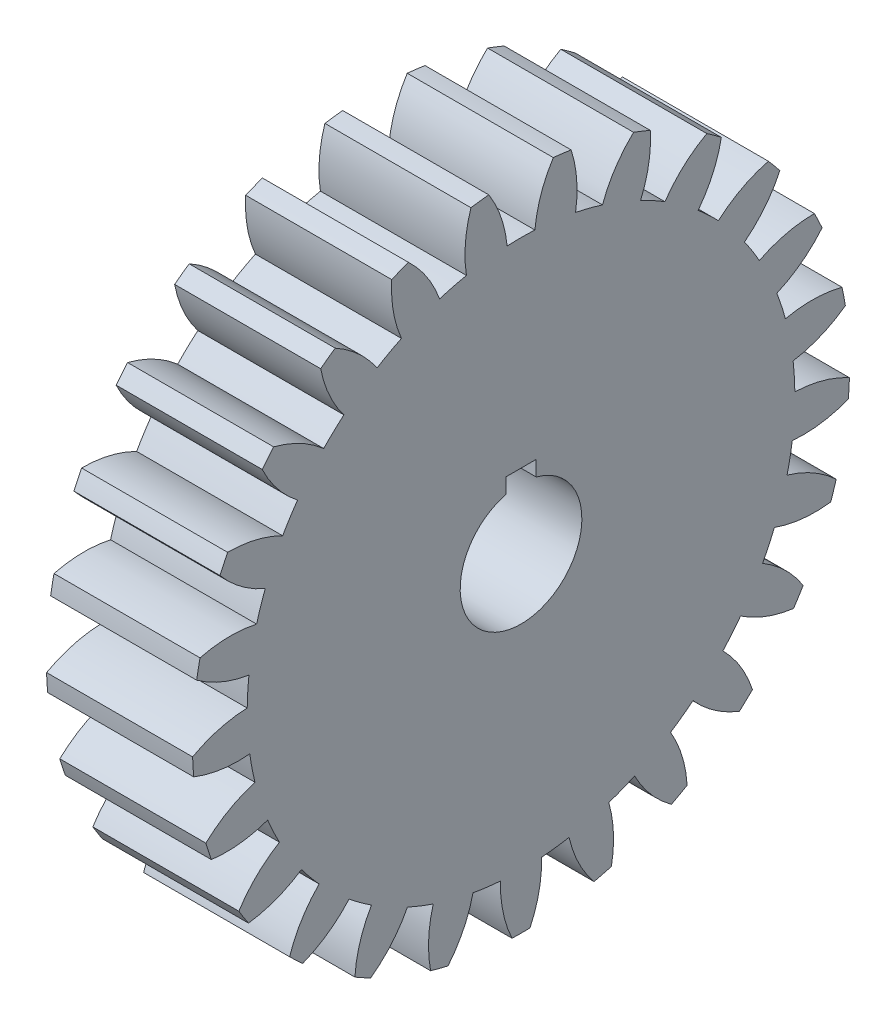
SolidWorks part; units mm, degrees
ref_plane "Plane1" through (0, 0, 0) normal (0, 0, 1) x (1, 0, 0)
ref_plane "Plane2" through (0, 0, 0) normal (0, 1, 0) x (1, 0, 0)
ref_plane "Plane3" through (0, 0, 0) normal (1, 0, 0) x (0, 0, -1)
other "Configuration Table"
sketch "HoldingSke" plane through (0, 0, 0) normal (0, 1, 0) x (1, 0, 0)
  line L0 (0, 0) -> (11.5101, -5.3673)
  line L1 (-15, 0) -> (100, 0) construction
  line L2 (0, 0) -> (-2.1039, 2.3779)
  line L3 (0, 0) -> (-11.863, 4.5341)
  line L4 (0, 0) -> (7.8269, 3.6497)
  line L5 (0, 0) -> (-47.5972, -17.7524)
  line L6 (0, 0) -> (-252.6679, -170.4757)
  line L7 (-2.1039, 2.3779) -> (63.5041, 300.0332)
  line L8 (-76.2, 54.61) -> (205.6384, 54.61)
  line L9 (-67.7845, 28.3722) -> (-49.3413, 33.142)
  line L10 (-76.2, 71.12) -> (104.1128, 71.12)
  line L11 (0, 0) -> (-304.8, 0)
  line L12 (-76.2, 101.6) -> (-74.295, 101.6)
  line L13 (24.9733, 27.94) -> (52.9518, 28.4284)
  line L14 (24.9733, 27.94) -> (24.9746, 27.94)
  line L15 (24.9733, 27.94) -> (100.4006, 29.5858)
  circle A0 centre (0, 0) radius 127
  circle A1 centre (0, 0) radius 38.1
  circle A2 centre (0, 0) radius 38.1
  circle A3 centre (0, 0) radius 127
  dimension "MHD" = 76.2
  dimension "Hub_dia" = 76.2
  dimension "Bore" = 254
  dimension "MBD" = 254
  dimension "Num_teeth" = 25
  dimension "Pitch" = 12.7
  dimension "Overall_len" = 50.8
  dimension "Show_teeth" = 25
  dimension "Thickness" = 304.8
  dimension "OAL" = 304.8001
  dimension "T_dim" = 281.8384
  dimension "Ap" = 14.5
  dimension "H" = 19.05
  dimension "Pitch_radius" = 180.3128
  dimension "Width" = 304.8
  dimension "Backlash" = 1.905
  dimension "Addendum_fac" = 1
  dimension "Dedendum_fac" = 1.25
  dimension "Clearance_fac" = 0.25
  dimension "Dedendum_add" = 0.0013
sketch "BasProSke" plane through (0, 0, 0) normal (0, 1, 0) x (1, 0, 0)
  line L0 (-10, 0) -> (60, 0) construction
  line L1 (0, 0) -> (0, 685.8)
  line L2 (0, 0) -> (304.8, 0)
  line L3 (304.8, 0) -> (304.8, 685.8)
  line L4 (304.8, 685.8) -> (0, 685.8)
  dimension "Thickness" = 304.8
  dimension "Diameter" = 1371.6
revolve "Base-Revolve" add sketch "BasProSke" angle 360 about L0
sketch "TooCutSke" plane through (0, 0, 0) normal (1, 0, 0) x (0, 0, -1)
  line L1 (0, 0) -> (0, 107) construction
  line L2 (0, 0) -> (-43.2046, 633.5285) construction
  line L3 (0, 0) -> (-158.9095, 1257.8981) construction
  line L4 (-43.2046, 633.5285) -> (-79.4547, 628.949) construction
  arc A0 (28.9619, 570.7644) -> (-28.9619, 570.7644) centre (0, 0) ccw
  arc A1 (67.344, 682.511) -> (-67.344, 682.511) centre (0, 0) ccw
  circle A2 centre (0, 0) radius 635 construction
  circle A3 centre (0, 0) radius 614.7738 construction
  arc A4 (-28.9619, 570.7644) -> (-67.344, 682.511) centre (-281.7896, 546.3894) ccw
  arc A5 (67.344, 682.511) -> (28.9619, 570.7644) centre (281.7896, 546.3894) ccw
  dimension "Root_dia" = 1142.9975
  dimension "Overcut_dia" = 1371.6508
  dimension "Pitch_dia" = 1270
  dimension "Base_dia" = 1229.5475
  dimension "Flank_rad" = 254
  dimension "Half_ang" = 7.2
  dimension "Half_CT" = 36.5382
extrude "ToothCut" cut sketch "TooCutSke" along normal through all
fillet "Breaks" [suppressed] radius 1.016
fillet "RootFillets" [suppressed] radius 12.7013
pattern_circular "TeethCuts" count 25 every 14.4 about axis through (-10, 0, 0) along (1, 0, 0) of "ToothCut", "RootFillets", "Breaks"
sketch "HubNeaOneSke" plane through (0, 0, 0) normal (-1, 0, 0) x (0, 0, 1)
  circle A0 centre (0, 0) radius 38.1
  dimension "Diameter" = 76.2
extrude "HubNearOne" [suppressed] add sketch "HubNeaOneSke" along normal blind 25.4001
sketch "HubNeaBotSke" plane through (0, 0, 0) normal (-1, 0, 0) x (0, 0, 1)
  circle A0 centre (0, 0) radius 38.1
  dimension "Diameter" = 76.2
extrude "HubNearBoth" [suppressed] add sketch "HubNeaBotSke" along normal blind 12.7
ref_plane "FarPln" through (304.8, 0, 0) normal (1, 0, 0) x (0, 0, -1)
sketch "HubFarSke" plane through (304.8, 0, 0) normal (1, 0, 0) x (0, 0, -1)
  circle A0 centre (0, 0) radius 38.1
  dimension "Diameter" = 76.2
extrude "HubFar" [suppressed] add sketch "HubFarSke" along normal blind 12.7
sketch "BorSke" plane through (0, 0, 0) normal (1, 0, 0) x (0, 0, -1)
  circle A0 centre (0, 0) radius 127
  dimension "Diameter" = 254
extrude "Bore" cut sketch "BorSke" along normal mid plane 609.6001
sketch "KeySke" plane through (0, 0, 0) normal (1, 0, 0) x (0, 0, -1)
  line L0 (-31.75, 0) -> (-31.75, 154.8384)
  line L1 (-31.75, 154.8384) -> (31.75, 154.8384)
  line L2 (31.75, 154.8384) -> (31.75, 0)
  line L3 (0, 0) -> (0, 34) construction
  line L4 (-31.75, 0) -> (31.75, 0)
  dimension "Offset" = 154.8384
  dimension "Width" = 63.5
extrude "Keyway" cut sketch "KeySke" along normal mid plane 609.6001
pattern_circular "Keyway2" [suppressed] count 2 every 90 about axis through (-10, 0, 0) along (1, 0, 0)
equation "' \"Pitch@HoldingSke\" = 4"
equation "' \"Num_teeth@HoldingSke\" = 12"
equation "' \"Ap@HoldingSke\" =  20"
equation "' \"Ap@HoldingSke\" = 20"
equation "' \"Width@HoldingSke\" = 0.5"
equation "' \"Hub_dia@HoldingSke\"= 1"
equation "' \"Hub_dia@HoldingSke\" = 1"
equation "' \"Overall_len@HoldingSke\" = 1.0"
equation "' \"Bore@HoldingSke\" = 0.75"
equation "' \"T_dim@HoldingSke\" = 0.85"
equation "' \"Width@KeySke\" = 0.25"
equation "' \"Show_teeth@HoldingSke\" = 13"
equation "' \"Backlash@HoldingSke\" = 0.009"
equation "' \"Addendum_fac@HoldingSke\" = 1.0"
equation "' \"Dedendum_fac@HoldingSke\" = 1.25"
equation "' \"Dedendum_add@HoldingSke\" = 0.00005"
equation "' \"Clearance_fac@HoldingSke\" = 0.25"
equation "' \"Pitch@HoldingSke\" = 0.5"
equation "' \"Num_teeth@HoldingSke\" = 23"
equation "' \"Show_teeth@HoldingSke\" = 23"
equation "' \"Backlash@HoldingSke\" = 0.0375"
equation "\"Overcut_dia@TooCutSke\" = (\"Num_teeth@HoldingSke\" + 2 * \"Addendum_fac@HoldingSke\") / \"Pitch@HoldingSke\" + 0.002"
equation "\"Pitch_dia@TooCutSke\" = \"Num_teeth@HoldingSke\" / \"Pitch@HoldingSke\""
equation "\"Base_dia@TooCutSke\" = \"Num_teeth@HoldingSke\" / \"Pitch@HoldingSke\" * cos((\"Ap@HoldingSke\"  * 3.14159265 / 180))"
equation "\"Root_dia@TooCutSke\" = (\"Num_teeth@HoldingSke\" + 2) / \"Pitch@HoldingSke\" - 2 * (\"Addendum_fac@HoldingSke\" + \"Dedendum_fac@HoldingSke\") / \"Pitch@HoldingSke\" - \"Dedendum_add@HoldingSke\" * 2"
equation "\"Half_ang@TooCutSke\" = 180 / \"Num_teeth@HoldingSke\""
equation "\"Half_CT@TooCutSke\" = \"Num_teeth@HoldingSke\" / \"Pitch@HoldingSke\" * sin((3.14159265 / 2 / \"Num_teeth@HoldingSke\")) / 2 - 7 * \"Backlash@HoldingSke\" / 4"
equation "\"Flank_rad@TooCutSke\" = \"Num_teeth@HoldingSke\" / \"Pitch@HoldingSke\" / 5"
equation "\"Radius@RootFillets\" = \"Clearance_fac@HoldingSke\" / \"Pitch@HoldingSke\" + \"Dedendum_add@HoldingSke\""
equation "\"Break_rad@Breaks\" = 0.02 / \"Pitch@HoldingSke\""
equation "\"Thickness@HoldingSke\" = \"Width@HoldingSke\""
equation "\"OAL@HoldingSke\" = \"Thickness@HoldingSke\""
equation "\"MHD@HoldingSke\" = (\"Num_teeth@HoldingSke\" + 2) / \"Pitch@HoldingSke\" - 2 * (\"Addendum_fac@HoldingSke\" + \"Dedendum_fac@HoldingSke\")  / \"Pitch@HoldingSke\" - \"Dedendum_add@HoldingSke\" * 2"
equation "\"MBD@HoldingSke\" = (\"Num_teeth@HoldingSke\" + 2) / \"Pitch@HoldingSke\" - 2 * (\"Addendum_fac@HoldingSke\" + \"Dedendum_fac@HoldingSke\")  / \"Pitch@HoldingSke\" - \"Dedendum_add@HoldingSke\" * 2 - 0.002"
equation "\"MHD@HoldingSke\" = ((sgn( \"MHD@HoldingSke\" - \"Hub_dia@HoldingSke\" )-1)*( \"MHD@HoldingSke\" - \"Hub_dia@HoldingSke\" ))/-2+ \"Hub_dia@HoldingSke\""
equation "\"MBD@HoldingSke\" = ((sgn( \"MBD@HoldingSke\" - \"Bore@HoldingSke\" )-1)*( \"MBD@HoldingSke\" - \"Bore@HoldingSke\" ))/-2+ \"Bore@HoldingSke\""
equation "\"OAL@HoldingSke\" = ((sgn( \"OAL@HoldingSke\" - \"Overall_len@HoldingSke\" )+1)*( \"OAL@HoldingSke\" - \"Overall_len@HoldingSke\" ))/2 + \"Overall_len@HoldingSke\" + 0.000002"
equation "\"Num_teeth@TeethCuts\" = int( \"Show_teeth@HoldingSke\" ) + 1"
equation "\"Num_teeth@TeethCuts\" = ((sgn( \"Num_teeth@TeethCuts\" - \"Num_teeth@HoldingSke\" )-1)*( \"Num_teeth@TeethCuts\" - \"Num_teeth@HoldingSke\" ))/-2+ \"Num_teeth@HoldingSke\""
equation "\"Num_teeth@TeethCuts\" = ((sgn( \"Num_teeth@TeethCuts\" - 2.0)+1)*( \"Num_teeth@TeethCuts\" - 2.0))/2 +2.0"
equation "\"Angle@TeethCuts\" = 360.0 / \"Num_teeth@HoldingSke\""
equation "\"Diameter@BasProSke\" = (\"Num_teeth@HoldingSke\" + 2 * \"Addendum_fac@HoldingSke\") / \"Pitch@HoldingSke\""
equation "\"Thickness@BasProSke\"  = \"Thickness@HoldingSke\""
equation "' \"Fillet_rad@BasProSke\" =  \"Thickness@HoldingSke\" * 0.05"
equation "' \"Fillet_rad@BasProSke\" = \"Thickness@HoldingSke\" * 0.05"
equation "\"MHD@HoldingSke\" = ((sgn( \"MHD@HoldingSke\" - \"Root_dia@TooCutSke\" )-1)*( \"MHD@HoldingSke\" - \"Root_dia@TooCutSke\" ))/-2+ \"Root_dia@TooCutSke\""
equation "\"Diameter@HubNeaOneSke\" = \"MHD@HoldingSke\""
equation "\"Length@HubNearOne\" = \"OAL@HoldingSke\" - \"Thickness@BasProSke\""
equation "\"Diameter@HubNeaBotSke\" = \"MHD@HoldingSke\""
equation "\"Length@HubNearBoth\" = ( \"OAL@HoldingSke\" - \"Thickness@BasProSke\" ) / 2.0"
equation "\"Thickness@FarPln\" = \"Thickness@BasProSke\""
equation "\"Diameter@HubFarSke\" = \"MHD@HoldingSke\""
equation "\"Length@HubFar\" = ( \"OAL@HoldingSke\" - \"Thickness@BasProSke\" ) / 2.0"
equation "\"Diameter@BorSke\" = \"MBD@HoldingSke\""
equation "\"D1@Bore\" = \"OAL@HoldingSke\" * 2.0"
equation "\"D1@Keyway\" = \"OAL@HoldingSke\" * 2.0"
equation "\"Offset@KeySke\" = \"T_dim@HoldingSke\" - \"MBD@HoldingSke\" / 2.0"
